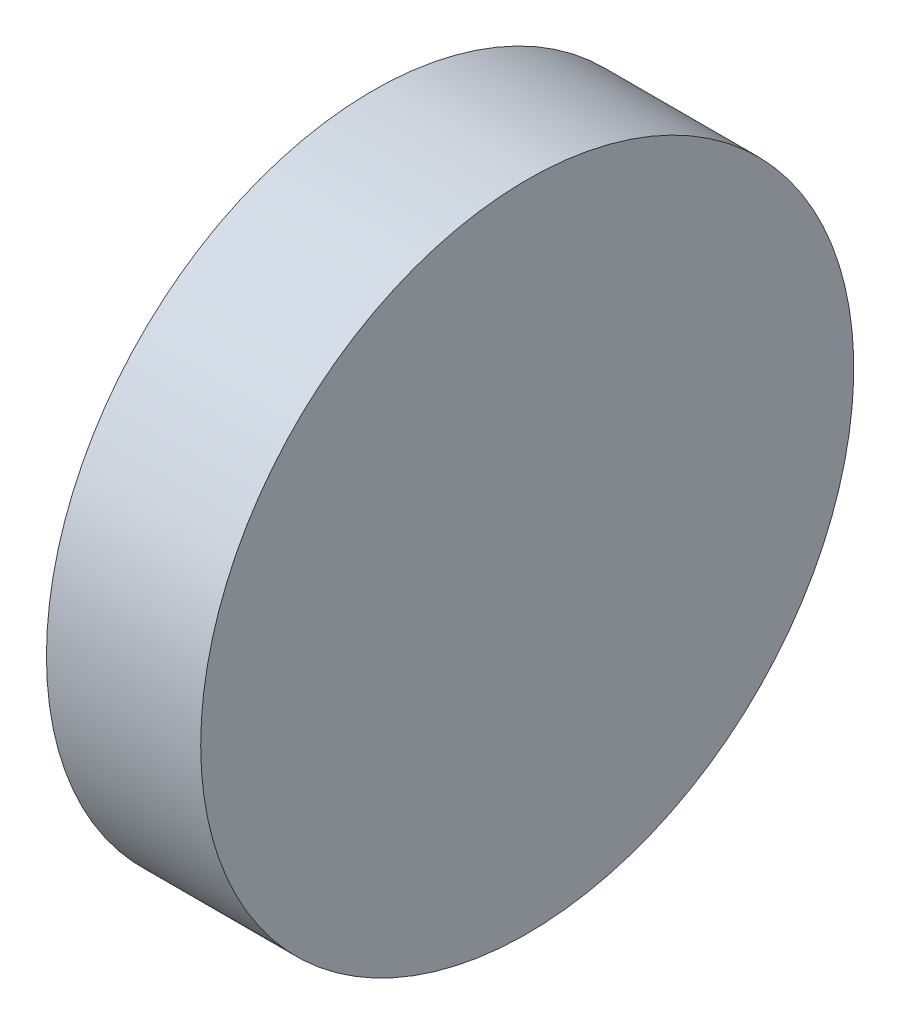
SolidWorks part; units mm, degrees
ref_plane "前视基准面" through (0, 0, 0) normal (0, 0, 1) x (1, 0, 0)
ref_plane "上视基准面" through (0, 0, 0) normal (0, 1, 0) x (1, 0, 0)
ref_plane "右视基准面" through (0, 0, 0) normal (1, 0, 0) x (0, 0, -1)
sketch "草图1" plane through (0, 0, 0) normal (0, 0, 1) x (1, 0, 0)
  line L0 (263.0933, 77.2932) -> (279.1235, 77.2932) construction
  line L1 (268.8168, 77.2932) -> (268.8168, 89.9932)
  line L2 (274.8168, 77.2932) -> (274.8168, 89.9932)
  line L3 (268.8168, 77.2932) -> (274.8168, 77.2932)
  line L4 (268.8168, 89.9932) -> (274.8168, 89.9932)
  dimension "D1" = 6
  dimension "D2" = 12.7
revolve "旋转1" add sketch "草图1" angle 360 about L0
